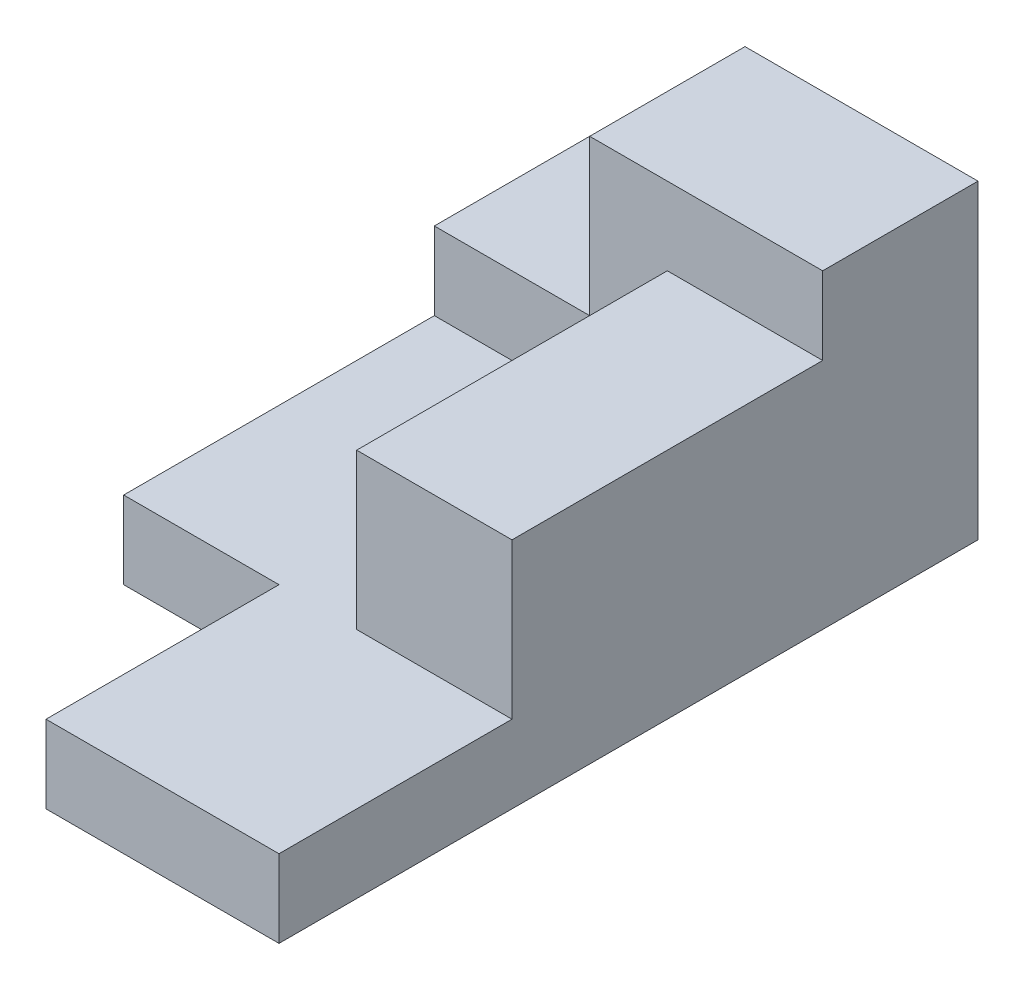
SolidWorks part; units mm, degrees
ref_plane "Front Plane" through (0, 0, 0) normal (0, 0, 1) x (1, 0, 0)
ref_plane "Top Plane" through (0, 0, 0) normal (0, 1, 0) x (1, 0, 0)
ref_plane "Right Plane" through (0, 0, 0) normal (1, 0, 0) x (0, 0, -1)
sketch "Sketch1" plane through (0, 0, 0) normal (0, 1, 0) x (1, 0, 0)
  line L1 (-30.2326, 23.8372) -> (19.7674, 23.8372)
  line L2 (-30.2326, 23.8372) -> (-30.2326, -66.1628)
  line L3 (-30.2326, -66.1628) -> (19.7674, -66.1628)
  line L4 (19.7674, 23.8372) -> (19.7674, -66.1628)
  dimension "D1" = 50
  dimension "D2" = 90
extrude "Boss-Extrude1" add sketch "Sketch1" along normal blind 10
sketch "Sketch2" plane through (0, 10, 0) normal (0, 1, 0) x (1, 0, 0)
  line L1 (-30.2326, 23.8372) -> (-30.2326, -66.1628) construction
  line L2 (-30.2326, -66.1628) -> (19.7674, -66.1628) construction
  line L3 (-30.2326, -36.1628) -> (-10.2326, -36.1628)
  line L4 (-30.2326, -36.1628) -> (-30.2326, -66.1628)
  line L5 (-30.2326, -66.1628) -> (-10.2326, -66.1628)
  line L6 (-10.2326, -36.1628) -> (-10.2326, -66.1628)
  dimension "D2" = 20
extrude "Cut-Extrude1" cut sketch "Sketch2" against normal through all both and the other way through all
ref_plane "Plane2" through (0, 10, 0) normal (0, 1, 0) x (1, 0, 0)
sketch "Sketch5" plane through (0, 10, 0) normal (0, 1, 0) x (1, 0, 0)
  line L1 (-30.2326, 23.8372) -> (19.7674, 23.8372)
  line L2 (-30.2326, 23.8372) -> (-30.2326, 3.8372)
  line L3 (-30.2326, 3.8372) -> (19.7674, 3.8372)
  line L4 (19.7674, 23.8372) -> (19.7674, 3.8372)
  dimension "D1" = 20
  dimension "D2" = 50
extrude "Boss-Extrude3" add sketch "Sketch5" along normal blind 10
ref_plane "Plane3" through (0, 20, 0) normal (0, 1, 0) x (1, 0, 0)
sketch "Sketch6" plane through (0, 20, 0) normal (0, 1, 0) x (1, 0, 0)
  line L0 (-30.2326, 3.8372) -> (-10.2326, 3.8372) construction
  line L1 (-30.2326, 3.8372) -> (19.7674, 3.8372) construction
  line L3 (-10.2326, 3.8372) -> (19.7674, 3.8372)
  line L4 (-10.2326, 3.8372) -> (-10.2326, 23.8372)
  line L5 (-10.2326, 23.8372) -> (19.7674, 23.8372)
  line L6 (19.7674, 3.8372) -> (19.7674, 23.8372)
  dimension "D1" = 20
extrude "Boss-Extrude4" add sketch "Sketch6" along normal blind 20
sketch "Sketch7" plane through (0, 10, 0) normal (0, 1, 0) x (1, 0, 0)
  line L1 (19.7674, 3.8372) -> (-0.2326, 3.8372)
  line L2 (19.7674, 3.8372) -> (19.7674, -36.1628)
  line L3 (19.7674, -36.1628) -> (-0.2326, -36.1628)
  line L4 (-0.2326, 3.8372) -> (-0.2326, -36.1628)
  dimension "D1" = 40
  dimension "D2" = 20
extrude "Boss-Extrude5" add sketch "Sketch7" along normal blind 20
